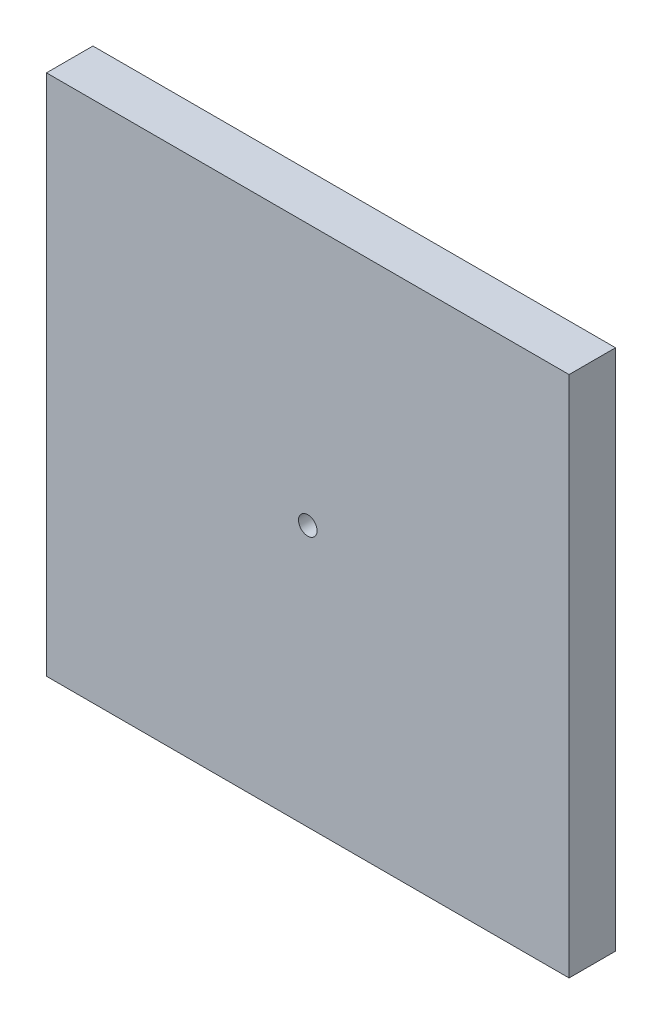
SolidWorks part; units mm, degrees
ref_plane "Front Plane" through (0, 0, 0) normal (0, 0, 1) x (1, 0, 0)
ref_plane "Top Plane" through (0, 0, 0) normal (0, 1, 0) x (1, 0, 0)
ref_plane "Right Plane" through (0, 0, 0) normal (1, 0, 0) x (0, 0, -1)
sketch "Sketch1" plane through (0, 0, 0) normal (0, 0, 1) x (1, 0, 0)
  line L1 (0, 0) -> (45, 0)
  line L2 (0, 0) -> (0, 45)
  line L3 (0, 45) -> (45, 45)
  line L4 (45, 0) -> (45, 45)
  circle A0 centre (22.5, 22.5) radius 0.8
  point P8 (22.5, 22.5)
  point P10 (45, 22.5)
  point P11 (22.5, 45)
  point P14 (0, 0)
  dimension "D3" = 1.6
  dimension "D1" = 45
  dimension "D2" = 45
extrude "Boss-Extrude1" add sketch "Sketch1" along normal blind 4
